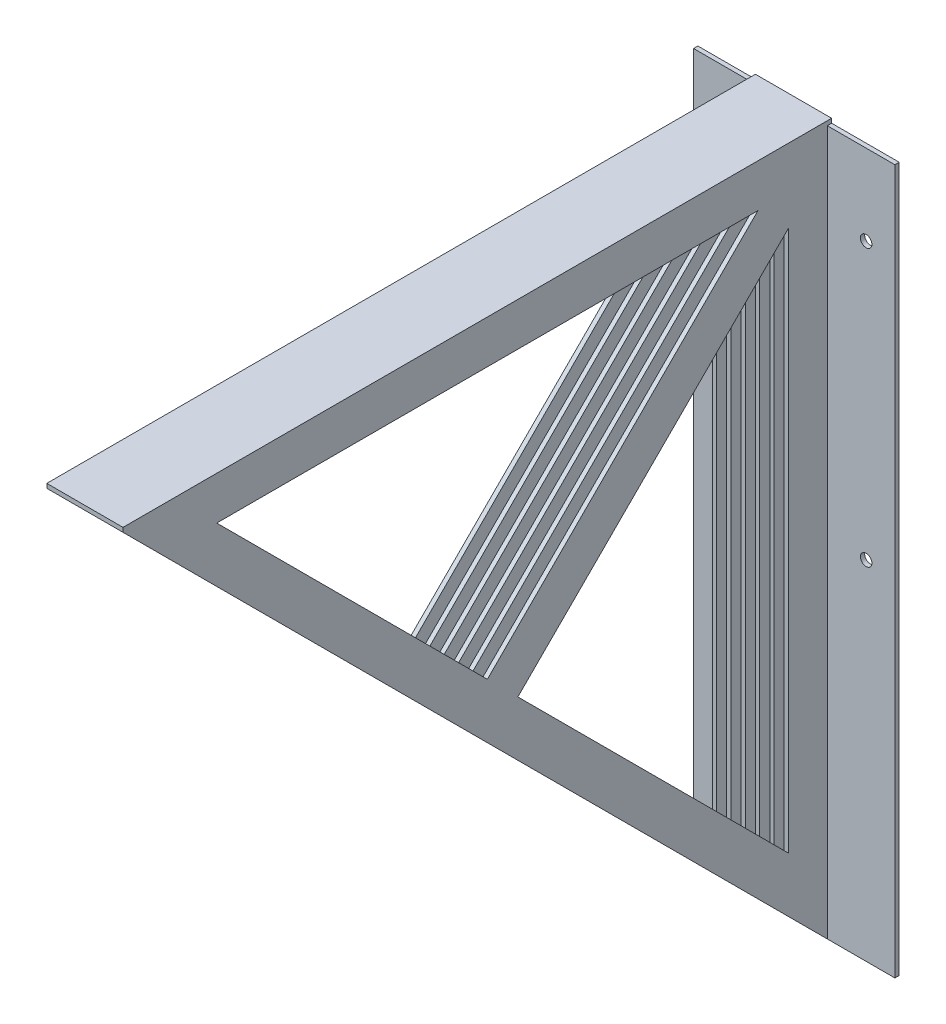
SolidWorks part; units mm, degrees
ref_plane "Front Plane" through (0, 0, 0) normal (0, 0, 1) x (1, 0, 0)
ref_plane "Top Plane" through (0, 0, 0) normal (0, 1, 0) x (1, 0, 0)
ref_plane "Right Plane" through (0, 0, 0) normal (1, 0, 0) x (0, 0, -1)
sketch "Sketch1" plane through (0, 0, 0) normal (1, 0, 0) x (0, 0, -1)
  line L0 (0, 0) -> (-250, 0) construction
  line L1 (-250, 0) -> (0, -250) construction
  line L2 (0, -250) -> (0, 0) construction
  point P3 (0, -368.1694)
  dimension "D1" = 250
sketch "Sketch2" plane through (0, 0, 0) normal (1, 0, 0) x (0, 0, -1)
  line L0 (0, 0) -> (-250, 0)
  line L1 (-250, 0) -> (0, -250)
  line L3 (0, -250) -> (0, 0)
  line L4 (-213.7868, -15) -> (-25.6066, -15)
  line L5 (-25.6066, -15) -> (-119.6967, -109.0901)
  line L6 (-119.6967, -109.0901) -> (-213.7868, -15)
  line L7 (-109.0901, -119.6967) -> (-15, -25.6066)
  line L8 (-15, -25.6066) -> (-15, -213.7868)
  line L9 (-15, -213.7868) -> (-109.0901, -119.6967)
  line L10 (-25.6066, -15) -> (-15, -25.6066) construction
  point P10 (-118.9596, -109.8272)
  dimension "D1" = 15
  dimension "D2" = 15
  dimension "D3" = 15
  dimension "D4" = 15
  dimension "D5" = 15
extrude "Boss-Extrude1" add sketch "Sketch2" along normal blind 1.5
sketch "Sketch3" plane through (1.5, 0, 0) normal (1, 0, 0) x (0, 0, -1)
  line L9 (6, -264.4853) -> (6, 6)
  line L10 (6, 6) -> (-264.4853, 6)
  line L11 (-264.4853, 6) -> (6, -264.4853)
  line L12 (-1.5, -246.3787) -> (-1.5, -1.5)
  line L13 (-246.3787, -1.5) -> (-1.5, -246.3787)
  line L14 (-1.5, -1.5) -> (-246.3787, -1.5)
  line L15 (-1.5, -246.3787) -> (-1.5, -1.5)
  line L16 (-246.3787, -1.5) -> (-1.5, -246.3787)
  line L17 (-1.5, -1.5) -> (-246.3787, -1.5)
  dimension "D1" = 1.5
  dimension "D2" = 7.5
extrude "Cut-Extrude2" cut sketch "Sketch3" against normal blind 1.5
sketch "Sketch4" plane through (0, 0, 1.5) normal (0, 0, -1) x (-1, 0, 0)
  line L1 (10, -1.5) -> (-40, -1.5)
  line L2 (10, -1.5) -> (10, -246.3787)
  line L3 (10, -246.3787) -> (-40, -246.3787)
  line L4 (-40, -1.5) -> (-40, -246.3787)
  line L5 (0, -246.3787) -> (-1.5, -246.3787) construction
  line L6 (0, -1.5) -> (-1.5, -1.5) construction
  line L7 (0, 0) -> (0, -250) construction
  point P8 (7.8488, 0)
  dimension "D1" = 50
  dimension "D2" = 10
extrude "Boss-Extrude2" add sketch "Sketch4" along normal blind 1.5
pattern_linear "LPattern1" count 6 spacing 5 along (1, 0, 0) of "Boss-Extrude1"
sketch "Sketch5" plane through (0, 0, 0) normal (-1, 0, 0) x (0, 0, 1)
  line L0 (0, -246.3787) -> (0, -250)
  line L1 (0, -250) -> (250, 0)
  line L2 (250, 0) -> (0, 0)
  line L3 (0, 0) -> (0, -1.5)
  line L4 (0, -1.5) -> (246.3787, -1.5)
  line L5 (246.3787, -1.5) -> (1.5, -246.3787)
  line L6 (1.5, -246.3787) -> (0, -246.3787)
extrude "Cut-Extrude3" cut sketch "Sketch5" against normal through all both and the other way through all
sketch "Sketch6" plane through (0, -1.5, 0) normal (0, 1, 0) x (1, 0, 0)
  line L1 (26.5, -246.3787) -> (0, -246.3787)
  line L2 (26.5, -246.3787) -> (26.5, 0)
  line L3 (26.5, 0) -> (0, 0)
  line L4 (0, -246.3787) -> (0, 0)
extrude "Boss-Extrude3" add sketch "Sketch6" along normal blind 1.5
sketch "Sketch8" plane through (0, 0, 1.5) normal (0, 0, 1) x (1, 0, 0)
  line L0 (40, -1.5) -> (40, -246.3787) construction
  line L1 (-20, -1.5) -> (50, -1.5)
  line L2 (-20, -1.5) -> (-20, -246.3787)
  line L3 (-20, -246.3787) -> (50, -246.3787)
  line L4 (50, -1.5) -> (50, -246.3787)
  line L5 (-10, -246.3787) -> (-10, -1.5) construction
  line L6 (-10, -1.5) -> (0, -1.5) construction
  line L7 (40, -246.3787) -> (-10, -246.3787) construction
  dimension "D1" = 10
  dimension "D2" = 10
extrude "Boss-Extrude9" add sketch "Sketch8" against normal blind 1.5
sketch "Sketch9" plane through (0, 0, 1.5) normal (0, 0, 1) x (1, 0, 0)
  line L0 (-20, -1.5) -> (0, -1.5) construction
  line L1 (-20, -1.5) -> (-20, -246.3787) construction
  circle A0 centre (-10, -29.5) radius 2
  circle A1 centre (-10, -125.5) radius 2
  circle A2 centre (40, -29.5) radius 2
  circle A3 centre (40, -125.5) radius 2
  point P10 (0, 0)
  point P11 (0, 0)
  dimension "D3" = 4
  dimension "D4" = 50
  dimension "D1" = 28
  dimension "D2" = 124
  dimension "D5" = 10
extrude "Cut-Extrude4" cut sketch "Sketch9" against normal blind 1.5
